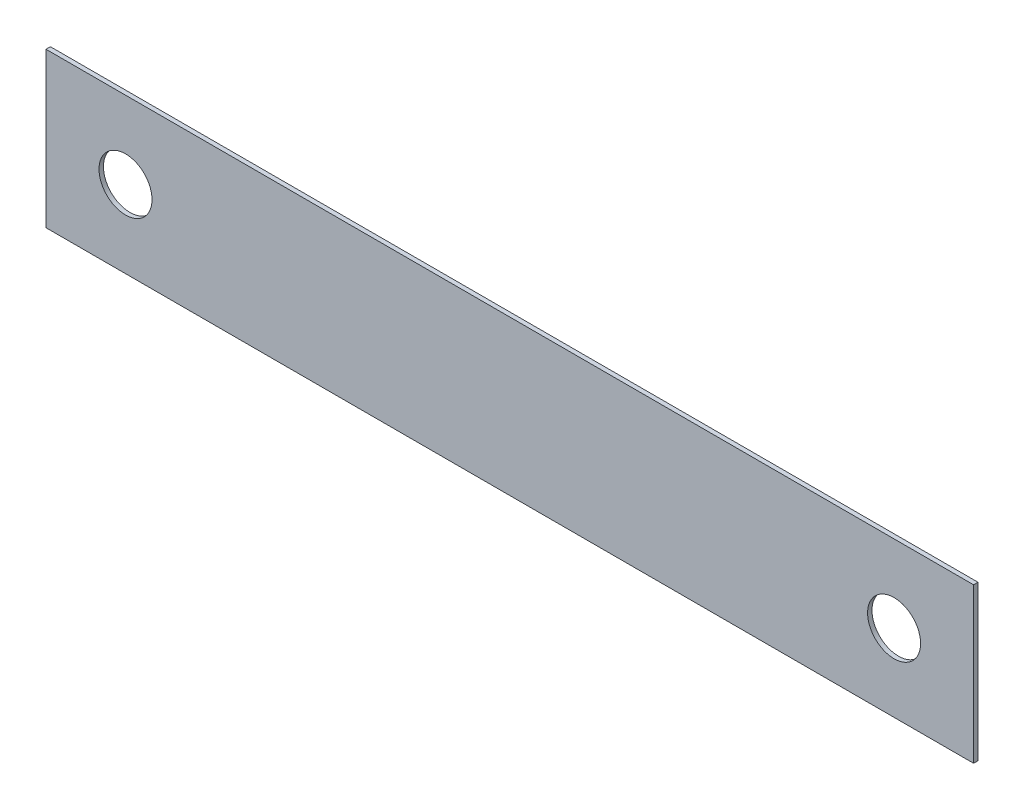
SolidWorks part; units mm, degrees
material "Chrome Stainless Steel"
ref_plane "Front Plane" through (0, 0, 0) normal (0, 0, 1) x (1, 0, 0)
ref_plane "Top Plane" through (0, 0, 0) normal (0, 1, 0) x (1, 0, 0)
ref_plane "Right Plane" through (0, 0, 0) normal (1, 0, 0) x (0, 0, -1)
sketch "Sketch1" plane through (0, 0, 0) normal (0, 0, 1) x (1, 0, 0)
  line L0 (-8.5816, 8.75) -> (109.137, 8.75) construction
  line L1 (0, 0) -> (105, 0)
  line L2 (0, 0) -> (0, 17.5)
  line L3 (0, 17.5) -> (105, 17.5)
  line L4 (105, 0) -> (105, 17.5)
  line L5 (52.5, 22.1465) -> (52.5, -2.8517) construction
  circle A0 centre (9, 8.75) radius 3
  circle A1 centre (96, 8.75) radius 3
  dimension "D3" = 6
  dimension "D1" = 105
  dimension "D2" = 17.5
  dimension "D5" = 87
extrude "Boss-Extrude1" add sketch "Sketch1" along normal blind 0.5
